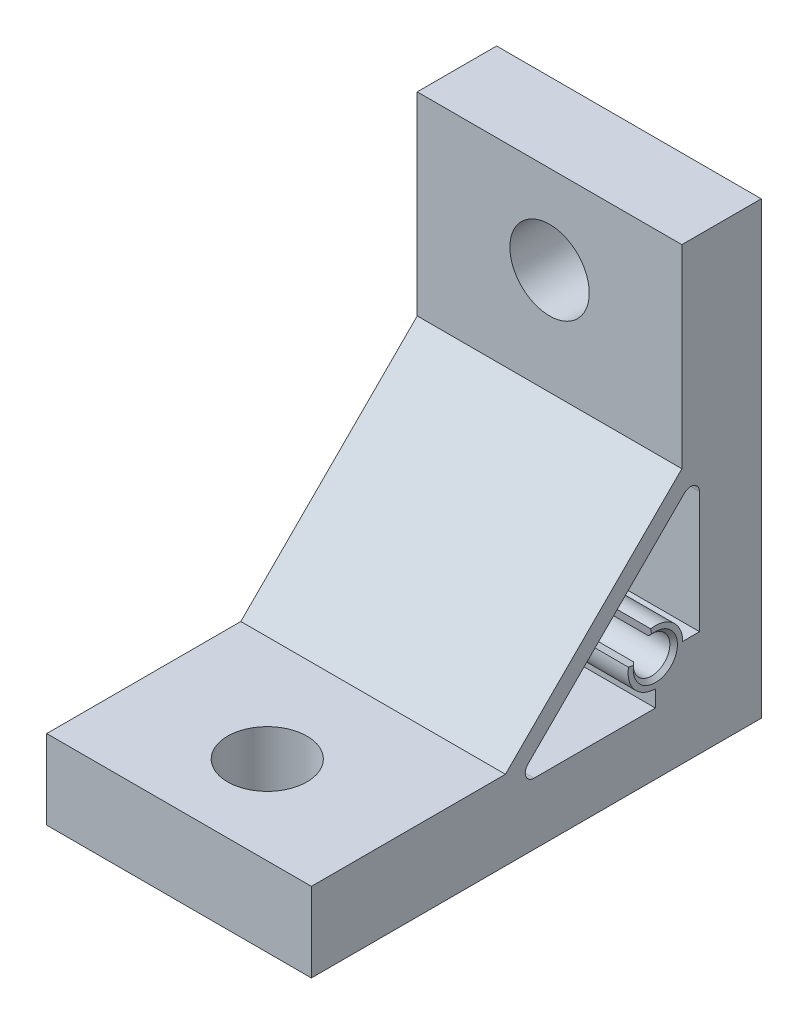
SolidWorks part; units mm, degrees
ref_plane "Front Plane" through (0, 0, 0) normal (0, 0, 1) x (1, 0, 0)
ref_plane "Top Plane" through (0, 0, 0) normal (0, 1, 0) x (1, 0, 0)
ref_plane "Right Plane" through (0, 0, 0) normal (1, 0, 0) x (0, 0, -1)
ref_plane "Plane1" through (15, 0, 0) normal (1, 0, 0) x (0, 0, -1)
sketch "Sketch1" plane through (15, 0, 0) normal (1, 0, 0) x (0, 0, -1)
  line L0 (0, 51) -> (-51, 51)
  line L1 (-51, 51) -> (-51, 0)
  line L2 (-51, 0) -> (0, 0)
  line L3 (0, 0) -> (0, 51)
extrude "Boss-Extrude1" add sketch "Sketch1" against normal blind 30
sketch "Sketch2" plane through (-15, 0, 0) normal (-1, 0, 0) x (0, 0, 1)
  line L0 (9, 51) -> (9, 29)
  line L1 (9, 29) -> (29, 9)
  line L2 (29, 9) -> (51, 9)
  line L3 (51, 9) -> (51, 51)
  line L4 (51, 51) -> (9, 51)
extrude "Cut-Extrude1" cut sketch "Sketch2" against normal through all
sketch "Sketch3" plane through (-15, 0, 0) normal (-1, 0, 0) x (0, 0, 1)
  line L0 (12, 8.9) -> (12, 7)
  line L1 (12, 7) -> (25.7574, 7)
  line L2 (26.4645, 8.7071) -> (8.7071, 26.4645)
  line L3 (7, 25.7574) -> (7, 12)
  line L4 (7, 12) -> (8.9, 12)
  line L5 (12.5383, 15.0529) -> (12.3647, 14.0681)
  line L6 (14.0681, 12.3647) -> (15.0529, 12.5383)
  arc A0 (15.0529, 12.5383) -> (12, 8.9) centre (12, 12) cw
  arc A1 (25.7574, 7) -> (26.4645, 8.7071) centre (25.7574, 8) ccw
  arc A2 (8.7071, 26.4645) -> (7, 25.7574) centre (8, 25.7574) ccw
  arc A3 (8.9, 12) -> (12.5383, 15.0529) centre (12, 12) cw
  arc A4 (12.3647, 14.0681) -> (14.0681, 12.3647) centre (12.5843, 12.5843) ccw
extrude "Cut-Extrude2" cut sketch "Sketch3" against normal through all
ref_plane "Plane2" through (0, 0, 12) normal (0, 0, 1) x (1, 0, 0)
sketch "Sketch4" plane through (0, 0, 12) normal (0, 0, 1) x (1, 0, 0)
  line L0 (-15, 14.067) -> (-15, 12)
  line L1 (-15, 12) -> (15, 12)
  line L2 (15, 12) -> (15, 14.067)
  line L3 (15, 14.067) -> (-15, 14.067)
  line L4 (-15, 12) -> (15, 12) construction
revolve "Cut-Revolve1" cut sketch "Sketch4" angle 360 about L4
hole_wizard "Ø9.0 (9) Diameter Hole1" positions "Sketch6" profile "Sketch5" hole size "Ø9.0" standard "ANSI Metric"
sketch "Sketch6" plane through (0, 0, 9) normal (0, 0, 1) x (1, 0, 0)
  point P0 (0, 41)
sketch "Sketch5" plane through (0, 41, 9) normal (1, 0, 0) x (0, -1, 0)
  line L0 (0, 0) -> (0, 9)
  line L1 (0, 9) -> (4.5, 9)
  line L2 (4.5, 9) -> (4.5, 0)
  line L5 (4.5, 0) -> (0, 0)
  line L11 (0, -6.35) -> (0, 107.95) construction
  dimension "Thru Hole Dia." = 9
  dimension "Thru Hole Depth" = 9
hole_wizard "Ø9.0 (9) Diameter Hole2" positions "Sketch8" profile "Sketch7" hole size "Ø9.0" standard "ANSI Metric"
sketch "Sketch8" plane through (0, 9, 0) normal (0, 1, 0) x (1, 0, 0)
  point P0 (0, -41)
sketch "Sketch7" plane through (0, 9, 41) normal (1, 0, 0) x (0, 0, 1)
  line L0 (0, 0) -> (0, 9)
  line L1 (0, 9) -> (4.5, 9)
  line L2 (4.5, 9) -> (4.5, 0)
  line L5 (4.5, 0) -> (0, 0)
  line L11 (0, -6.35) -> (0, 107.95) construction
  dimension "Thru Hole Dia." = 9
  dimension "Thru Hole Depth" = 9
chamfer "Chamfer1" distance 0.433 angle 45 2 edges at (15, 14.0598, 12.3148) (15, 10.5384, 10.5384)
